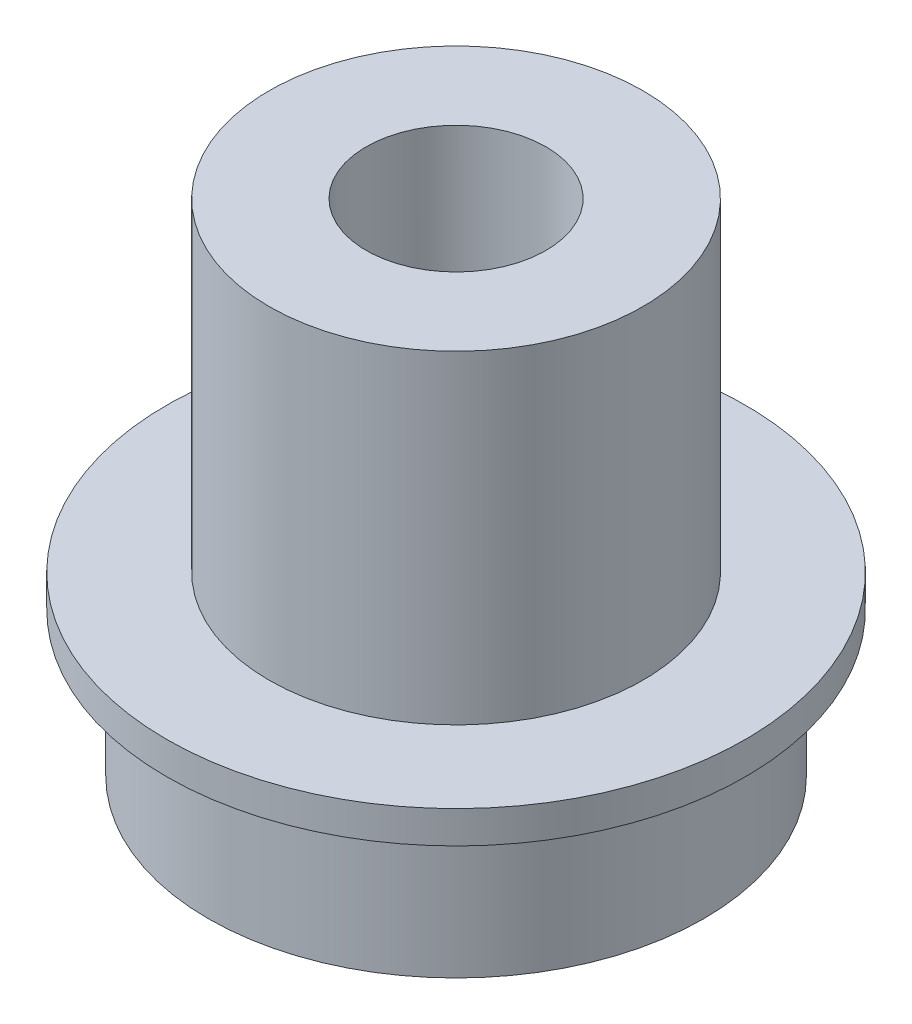
SolidWorks part; units mm, degrees
ref_plane "Front Plane" through (0, 0, 0) normal (0, 0, 1) x (1, 0, 0)
ref_plane "Top Plane" through (0, 0, 0) normal (0, 1, 0) x (1, 0, 0)
ref_plane "Right Plane" through (0, 0, 0) normal (1, 0, 0) x (0, 0, -1)
sketch "Sketch1" plane through (0, 0, 0) normal (0, 1, 0) x (1, 0, 0)
  circle A0 centre (0, 0) radius 8.7503
  circle A1 centre (0, 0) radius 3.175
  dimension "D1" = 17.5006
  dimension "D2" = 6.35
extrude "Boss-Extrude1" add sketch "Sketch1" along normal blind 5.08
sketch "Sketch2" plane through (0, 5.08, 0) normal (0, 1, 0) x (1, 0, 0)
  circle A0 centre (0, 0) radius 3.175
  circle A1 centre (0, 0) radius 10.2235
  dimension "D1" = 20.447
extrude "Boss-Extrude2" add sketch "Sketch2" along normal blind 1.143
sketch "Sketch3" plane through (0, 6.223, 0) normal (0, 1, 0) x (1, 0, 0)
  circle A0 centre (0, 0) radius 6.604
  dimension "D1" = 13.208
extrude "Boss-Extrude3" add sketch "Sketch3" along normal blind 11.43
sketch "Sketch4" plane through (0, 6.223, 0) normal (0, -1, 0) x (1, 0, 0)
  circle A0 centre (0, 0) radius 3.175
extrude "Cut-Extrude1" cut sketch "Sketch4" against normal through all
